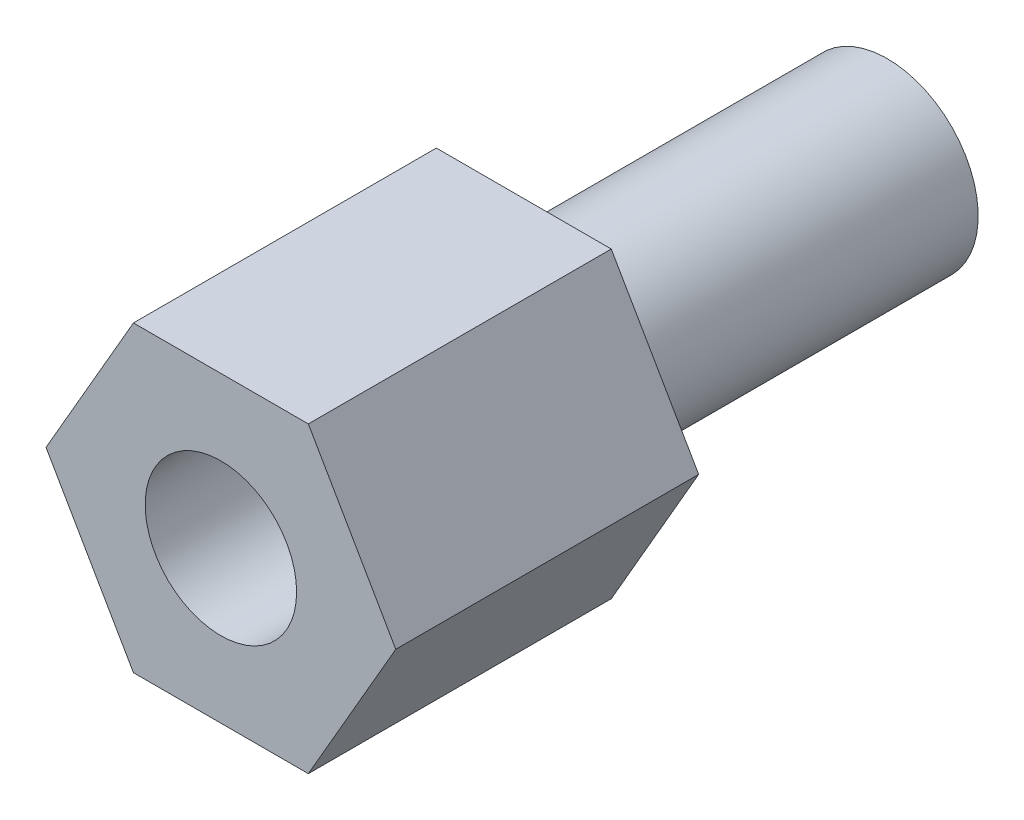
SolidWorks part; units mm, degrees
material "尼龍 6/10"
ref_plane "前基準面" through (0, 0, 0) normal (0, 0, 1) x (1, 0, 0)
ref_plane "上基準面" through (0, 0, 0) normal (0, 1, 0) x (1, 0, 0)
ref_plane "右基準面" through (0, 0, 0) normal (1, 0, 0) x (0, 0, -1)
sketch "草圖1" plane through (0, 0, 0) normal (0, 0, 1) x (1, 0, 0)
  line L1 (-1.4434, 2.5) -> (-2.8868, 0)
  line L2 (-2.8868, 0) -> (-1.4434, -2.5)
  line L3 (-1.4434, -2.5) -> (1.4434, -2.5)
  line L4 (1.4434, -2.5) -> (2.8868, 0)
  line L5 (2.8868, 0) -> (1.4434, 2.5)
  line L6 (1.4434, 2.5) -> (-1.4434, 2.5)
  circle A0 centre (0, 0) radius 2.5 construction
  dimension "D1" = 5
extrude "填料-伸長1" add sketch "草圖1" along normal blind 5
sketch "草圖4" plane through (0, 0, 0) normal (0, 0, -1) x (-1, 0, 0)
  circle A0 centre (0, 0) radius 1.5
  dimension "D1" = 3
extrude "填料-伸長2" add sketch "草圖4" along normal blind 6
hole_wizard "M3x0.5 螺紋孔1" positions "草圖2" profile "草圖3" tap size "M3x0.5" standard "Ansi Metric"
sketch "草圖2" plane through (0, 0, 5) normal (0, 0, 1) x (1, 0, 0)
  point P0 (0, 0)
sketch "草圖3" plane through (0, 0, 5) normal (1, 0, 0) x (0, -1, 0)
  line L0 (0, 0) -> (0, 8.2511)
  line L1 (0, 8.2511) -> (1.25, 7.5)
  line L2 (1.25, 7.5) -> (1.25, 0)
  line L5 (1.25, 0) -> (0, 0)
  line L10 (0, 8.2511) -> (-1.25, 7.5) construction
  line L11 (0, -6.35) -> (0, 107.95) construction
  dimension "螺孔鑽直徑" = 2.5
  dimension "螺孔鑽深度" = 7.5
  dimension "導頭角度" = 118
